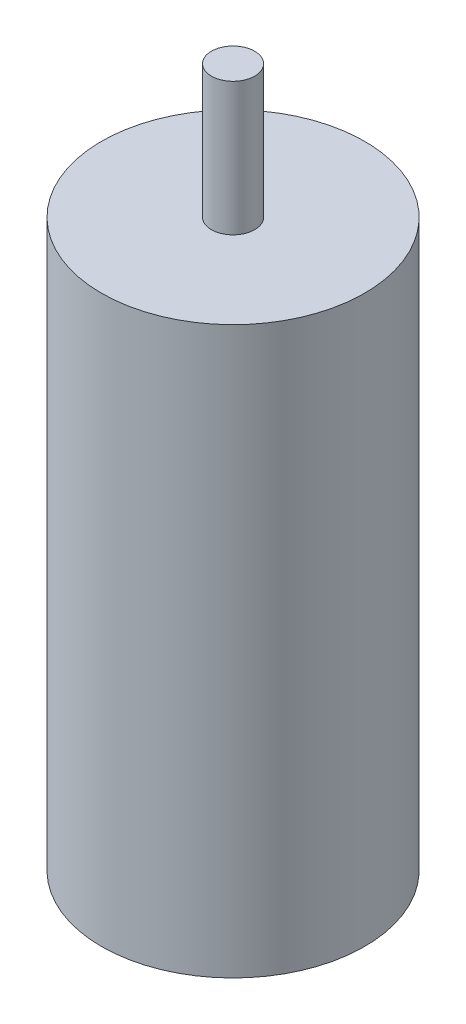
SolidWorks part; units mm, degrees
ref_plane "Front Plane" through (0, 0, 0) normal (0, 0, 1) x (1, 0, 0)
ref_plane "Top Plane" through (0, 0, 0) normal (0, 1, 0) x (1, 0, 0)
ref_plane "Right Plane" through (0, 0, 0) normal (1, 0, 0) x (0, 0, -1)
sketch "Sketch1" plane through (0, 0, 0) normal (0, 1, 0) x (1, 0, 0)
  circle A0 centre (0, 0) radius 12.0968
  dimension "D1" = 24.1935
ref_plane "Plane1" through (0, 52.0192, 0) normal (0, 1, 0) x (1, 0, 0)
extrude "Boss-Extrude1" add sketch "Sketch1" along normal up to surface (52.0192 mm away) up to plane "Plane1"
ref_plane "Plane2" through (0, 64.2493, 0) normal (0, 1, 0) x (1, 0, 0)
sketch "Sketch2" plane through (0, 52.0192, 0) normal (0, 1, 0) x (1, 0, 0)
  circle A0 centre (0, 0) radius 1.9875
  dimension "D1" = 3.9751
extrude "Boss-Extrude2" add sketch "Sketch2" along normal up to surface (12.2301 mm away) up to plane "Plane2"
